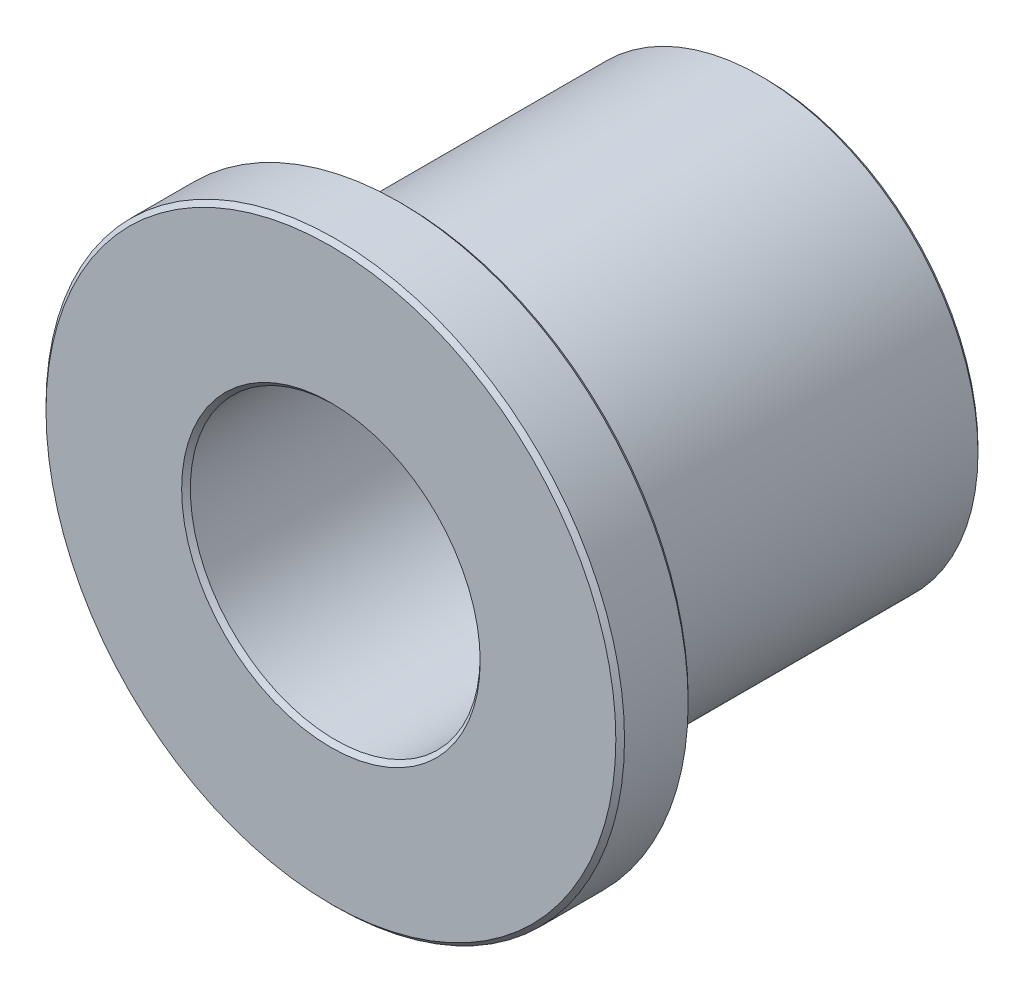
SolidWorks part; units mm, degrees
material "Tin Bearing Bronze"
ref_plane "Front" through (0, 0, 0) normal (0, 0, 1) x (1, 0, 0)
ref_plane "Top" through (0, 0, 0) normal (0, 1, 0) x (1, 0, 0)
ref_plane "Right" through (0, 0, 0) normal (1, 0, 0) x (0, 0, -1)
sketch "Sketch1" plane through (0, 0, 0) normal (0, 0, 1) x (1, 0, 0)
  circle A0 centre (0, 0) radius 6.3627
  circle A1 centre (0, 0) radius 9.5504
  circle A2 centre (0, 0) radius 12.7
  dimension "ID" = 12.7254
  dimension "OD" = 19.1008
  dimension "Flange OD" = 25.4
sketch "Sketch2" plane through (0, 0, 0) normal (1, 0, 0) x (0, 0, -1)
  line L0 (-9.525, -12.7) -> (9.525, -12.7) construction
  line L1 (0, 12.7) -> (0, -12.7) construction
  line L3 (-6.35, 9.5504) -> (9.525, 9.5504) construction
  point P3 (0, -12.7)
  point P7 (0, 9.5504)
  point P9 (-6.35, -12.7)
  point P10 (-9.525, 12.7)
  point P23 (0, 12.7)
  dimension "Flange Thickness" = 3.175
  dimension "Length" = 19.05
sketch "Sketch3" plane through (0, 0, 0) normal (0, 0, 1) x (1, 0, 0)
  circle A0 centre (0, 0) radius 12.7 construction
  circle A1 centre (0, 0) radius 12.7
  circle A2 centre (0, 0) radius 6.3627 construction
  circle A3 centre (0, 0) radius 6.3627
extrude "Boss-Extrude1" add sketch "Sketch3" against normal up to vertex (-6.35 mm away) from vertex at 9.525 starting at point (0, -12.7, 9.525)
sketch "Sketch4" plane through (0, 0, 0) normal (0, 0, 1) x (1, 0, 0)
  circle A0 centre (0, 0) radius 6.3627 construction
  circle A1 centre (0, 0) radius 9.5504 construction
  circle A2 centre (0, 0) radius 6.3627
  circle A3 centre (0, 0) radius 9.5504
extrude "Boss-Extrude2" add sketch "Sketch4" against normal up to vertex (9.525 mm away) from vertex at 6.35 starting at point (0, -12.7, 6.35)
chamfer "Chamfer1" distance 0.1909 angle 45 6 edges at (6.3627, 0, 9.525) (12.7, 0, 9.525) (12.7, 0, 6.35) (9.5504, 0, 6.35) (6.3627, 0, -9.525) (9.5504, 0, -9.525)
equation "\"D1@Chamfer1\"=\"ID@Sketch1\"*0.015"
